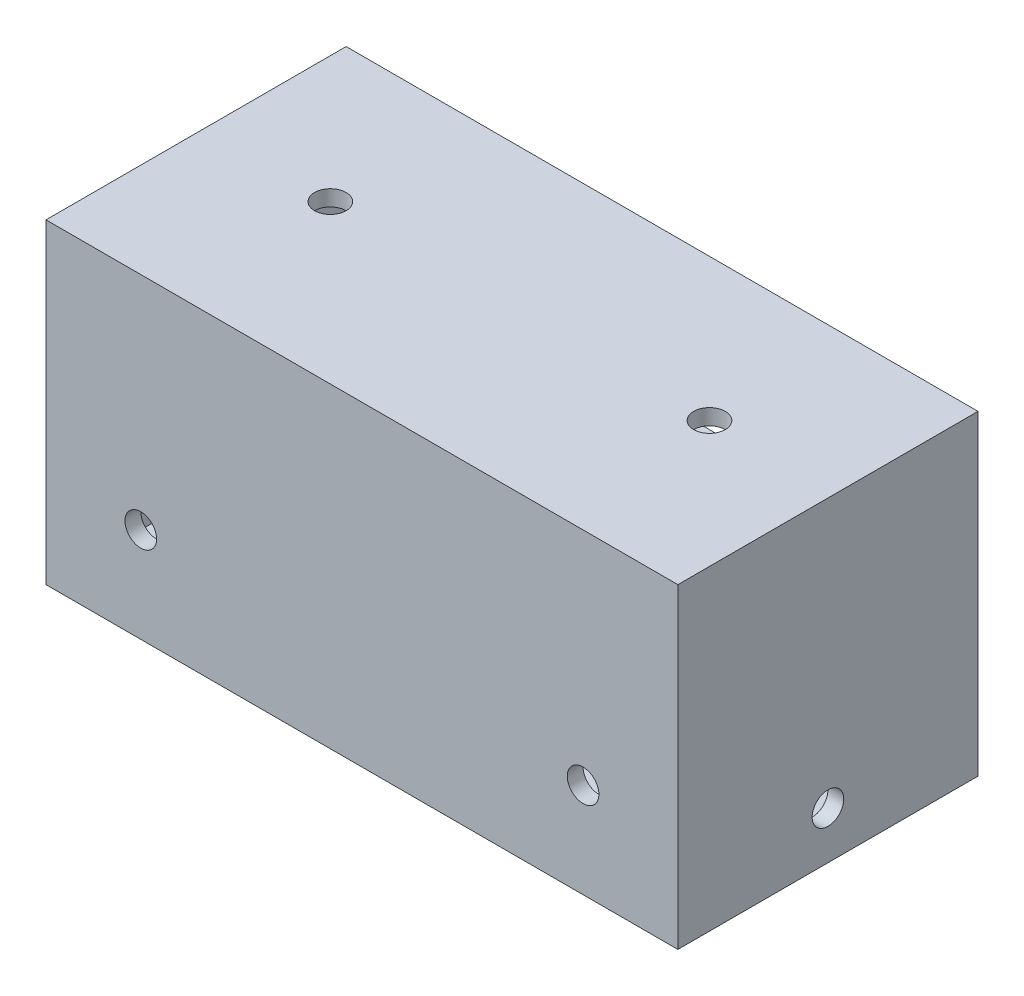
SolidWorks part; units mm, degrees
ref_plane "Front Plane" through (0, 0, 0) normal (0, 0, 1) x (1, 0, 0)
ref_plane "Top Plane" through (0, 0, 0) normal (0, 1, 0) x (1, 0, 0)
ref_plane "Right Plane" through (0, 0, 0) normal (1, 0, 0) x (0, 0, -1)
sketch "Sketch2" plane through (0, 0, 0) normal (0, 0, 1) x (1, 0, 0)
  line L1 (-100, 50) -> (100, 50)
  line L2 (-100, 50) -> (-100, -50)
  line L3 (-100, -50) -> (100, -50)
  line L4 (100, 50) -> (100, -50)
  line L5 (-100, 50) -> (100, -50) construction
  line L6 (-100, -50) -> (100, 50) construction
  line L7 (-95, -45) -> (95, -45)
  line L8 (-95, -45) -> (-95, 45)
  line L9 (-95, 45) -> (95, 45)
  line L10 (95, -45) -> (95, 45)
  line L11 (-95, -45) -> (95, 45) construction
  line L12 (-95, 45) -> (95, -45) construction
  line L13 (-95, -45) -> (-29.0331, -45)
  line L14 (-95, -45) -> (-95, -2.5)
  line L15 (-95, -2.5) -> (-29.0331, -2.5)
  line L16 (-29.0331, -45) -> (-29.0331, -2.5)
  line L17 (-95, 2.5) -> (-29.0331, 2.5)
  line L18 (-95, 2.5) -> (-95, 45)
  line L19 (-95, 45) -> (-29.0331, 45)
  line L20 (-29.0331, 2.5) -> (-29.0331, 45)
  point P0 (0, 0)
  point P6 (0, 0)
  dimension "D1" = 200
  dimension "D2" = 100
  dimension "D3" = 5
  dimension "D4" = 5
  dimension "D5" = 42.5
  dimension "D6" = 42.5
  dimension "D7" = 65.9669
extrude "Boss-Extrude1" add sketch "Sketch2" along normal blind 5 contours L20 L17 L8 L15 L16 L7 L10 L9 | L4 L1 L2 L3 L10 L7 L8 L9 | L7 L16 L15 L8 | L17 L20 L9 L8
sketch "Sketch4" plane through (0, 0, 0) normal (0, 0, -1) x (-1, 0, 0)
  line L0 (-100, 50) -> (-100, -50) construction
  line L1 (95, -45) -> (-95, -45)
  line L2 (95, -45) -> (95, 45)
  line L3 (95, 45) -> (-95, 45)
  line L4 (-95, -45) -> (-95, 45)
  line L5 (95, -45) -> (-95, 45) construction
  line L6 (95, 45) -> (-95, -45) construction
  line L7 (100, -50) -> (-100, -50) construction
  line L9 (95, -45) -> (35, -45)
  line L10 (95, -45) -> (95, -2.5)
  line L11 (95, -2.5) -> (35, -2.5)
  line L12 (35, -45) -> (35, -2.5)
  line L13 (95, 2.5) -> (35, 2.5)
  line L14 (95, 2.5) -> (95, 45)
  line L15 (95, 45) -> (35, 45)
  line L16 (35, 2.5) -> (35, 45)
  line L17 (30, -45) -> (-30, -45)
  line L18 (30, -45) -> (30, -2.5)
  line L19 (30, -2.5) -> (-30, -2.5)
  line L20 (-30, -45) -> (-30, -2.5)
  line L21 (30, 2.5) -> (-30, 2.5)
  line L22 (30, 2.5) -> (30, 45)
  line L23 (30, 45) -> (-30, 45)
  line L24 (-30, 2.5) -> (-30, 45)
  line L25 (-35, -45) -> (-95, -45)
  line L26 (-35, -45) -> (-35, -2.5)
  line L27 (-35, -2.5) -> (-95, -2.5)
  line L28 (-95, -45) -> (-95, -2.5)
  line L29 (-35, 2.5) -> (-95, 2.5)
  line L30 (-35, 2.5) -> (-35, 45)
  line L31 (-35, 45) -> (-95, 45)
  line L32 (-95, 2.5) -> (-95, 45)
  point P0 (0, 0)
  line M18 (-100, 50) -> (-100, -50)
  line M19 (-100, -50) -> (100, -50)
  line M20 (100, -50) -> (100, 50)
  line M21 (100, 50) -> (-100, 50)
  dimension "D1" = 5
  dimension "D2" = 5
  dimension "D3" = 42.5
  dimension "D4" = 42.5
  dimension "D5" = 60
  dimension "D6" = 60
  dimension "D7" = 42.5
  dimension "D8" = 5
  dimension "D9" = 5
  dimension "D10" = 42.5
  dimension "D11" = 60
  dimension "D12" = 60
  dimension "D13" = 5
  dimension "D14" = 5
  dimension "D15" = 42.5
  dimension "D16" = 42.5
extrude "Boss-Extrude2" add sketch "Sketch4" along normal blind 90 contours L1 L4 L3 L2 M21 M18 M19 M20 | L30 L29 L4 L27 L26 L1 L20 L19 L18 L12 L11 L2 L13 L16 L3 L22 L21 L24
sketch "Sketch5" plane through (-35, 0, 0) normal (-1, 0, 0) x (0, 0, 1)
  line L0 (0, 2.5) -> (0, 45) construction
  line L1 (-10, 12.5) -> (-80, 12.5)
  line L2 (-10, 12.5) -> (-10, 35)
  line L3 (-10, 35) -> (-80, 35)
  line L4 (-80, 12.5) -> (-80, 35)
  line L5 (-90, 2.5) -> (0, 2.5) construction
  line L6 (-90, 45) -> (0, 45) construction
  line L7 (-90, 2.5) -> (-90, 45) construction
  dimension "D1" = 10
  dimension "D2" = 10
  dimension "D3" = 10
  dimension "D4" = 10
extrude "Cut-Extrude1" cut sketch "Sketch5" against normal blind 90
sketch "Sketch6" plane through (-35, 0, 0) normal (-1, 0, 0) x (0, 0, 1)
  line L0 (-90, -45) -> (-90, -2.5) construction
  line L1 (-10, -35) -> (-80, -35)
  line L2 (-10, -35) -> (-10, -12.5)
  line L3 (-10, -12.5) -> (-80, -12.5)
  line L4 (-80, -35) -> (-80, -12.5)
  line L5 (-90, -45) -> (0, -45) construction
  line L6 (-90, -2.5) -> (0, -2.5) construction
  line L7 (0, -45) -> (0, -2.5) construction
  dimension "D1" = 10
  dimension "D2" = 10
  dimension "D3" = 10
  dimension "D4" = 10
extrude "Cut-Extrude2" cut sketch "Sketch6" against normal blind 90
sketch "Sketch7" plane through (0, -2.5, 0) normal (0, -1, 0) x (-1, 0, 0)
  line L0 (95, 90) -> (35, 90) construction
  line L1 (85, 10) -> (45, 10)
  line L2 (85, 10) -> (85, 80)
  line L3 (85, 80) -> (45, 80)
  line L4 (45, 10) -> (45, 80)
  line L5 (95, 0) -> (35, 0) construction
  line L6 (35, 90) -> (35, 0) construction
  line L7 (95, 90) -> (95, 0) construction
  dimension "D1" = 10
  dimension "D2" = 10
  dimension "D3" = 10
  dimension "D4" = 10
extrude "Cut-Extrude3" cut sketch "Sketch7" against normal blind 10
sketch "Sketch8" plane through (0, -2.5, 0) normal (0, -1, 0) x (-1, 0, 0)
  line L0 (30, 0) -> (-30, 0) construction
  line L1 (20, 10) -> (-20, 10)
  line L2 (20, 10) -> (20, 80)
  line L3 (20, 80) -> (-20, 80)
  line L4 (-20, 10) -> (-20, 80)
  line L5 (-30, 90) -> (-30, 0) construction
  line L6 (30, 90) -> (-30, 90) construction
  line L7 (30, 90) -> (30, 0) construction
  dimension "D1" = 10
  dimension "D2" = 10
  dimension "D3" = 10
  dimension "D4" = 10
extrude "Cut-Extrude4" cut sketch "Sketch8" against normal blind 10
sketch "Sketch9" plane through (0, -2.5, 0) normal (0, -1, 0) x (-1, 0, 0)
  line L0 (-35, 90) -> (-35, 0) construction
  line L1 (-45, 10) -> (-85, 10)
  line L2 (-45, 10) -> (-45, 80)
  line L3 (-45, 80) -> (-85, 80)
  line L4 (-85, 10) -> (-85, 80)
  line L5 (-35, 90) -> (-95, 90) construction
  line L6 (-35, 0) -> (-95, 0) construction
  line L7 (-95, 90) -> (-95, 0) construction
  dimension "D1" = 10
  dimension "D2" = 10
  dimension "D3" = 10
  dimension "D4" = 10
extrude "Cut-Extrude5" cut sketch "Sketch9" against normal blind 10
sketch "Sketch10" plane through (0, 0, -90) normal (0, 0, -1) x (-1, 0, 0)
  line L0 (30, -2.5) -> (-30, -2.5) construction
  line L1 (35, -45) -> (35, -2.5) construction
  line L2 (-100, -50) -> (100, -50) construction
  line L3 (100, -50) -> (100, 50) construction
  line L4 (0, 0) -> (0, -50) construction
  line L5 (0, 0) -> (100, 0) construction
  line L6 (-100, 50) -> (-100, -50) construction
  circle A0 centre (32.5, 0) radius 2
  circle A1 centre (97.5, -47.5) radius 2
  circle A2 centre (97.5, 47.5) radius 2
  circle A3 centre (-97.5, 47.5) radius 2
  circle A4 centre (-32.5, 0) radius 2
  circle A5 centre (-97.5, -47.5) radius 2
  dimension "D3" = 4
  dimension "D6" = 4
  dimension "D1" = 2.5
  dimension "D2" = 2.5
  dimension "D4" = 2.5
  dimension "D5" = 2.5
extrude "Cut-Extrude6" cut sketch "Sketch10" against normal blind 10
sketch "Sketch11" plane through (0, -50, 0) normal (0, -1, 0) x (-1, 0, 0)
  line L0 (100, -5) -> (-100, -5) construction
  line L3 (100, -5) -> (100, 90) construction
  line L8 (-100, -5) -> (-100, 90) construction
  circle A0 centre (60, 45) radius 5
  circle A1 centre (-60, 45) radius 5
  dimension "D1" = 10
  dimension "D6" = 10
  dimension "D2" = 50
  dimension "D3" = 50
  dimension "D4" = 40
  dimension "D5" = 40
extrude "Cut-Extrude7" cut sketch "Sketch11" against normal blind 150
sketch "Sketch12" plane through (-100, 0, 0) normal (-1, 0, 0) x (0, 0, 1)
  line L0 (-42.5, -50) -> (-42.5, 50) construction
  line L1 (5, -50) -> (-90, -50) construction
  line L2 (5, 50) -> (-90, 50) construction
  circle A0 centre (-42.5, -35) radius 5
  dimension "D1" = 10
  dimension "D2" = 15
extrude "Cut-Extrude8" cut sketch "Sketch12" against normal blind 10
sketch "Sketch13" plane through (100, 0, 0) normal (1, 0, 0) x (0, 0, -1)
  line L0 (42.5, -50) -> (42.5, 50) construction
  line L1 (-5, -50) -> (90, -50) construction
  line L2 (-5, 50) -> (90, 50) construction
  circle A0 centre (42.5, -35) radius 5
  dimension "D2" = 10
  dimension "D1" = 15
extrude "Cut-Extrude9" cut sketch "Sketch13" against normal blind 10
sketch "Sketch14" plane through (0, 0, 5) normal (0, 0, 1) x (1, 0, 0)
  line L0 (0, 50) -> (0, -50) construction
  line L1 (-100, 50) -> (100, 50) construction
  line L2 (-100, -50) -> (100, -50) construction
  line L3 (-100, 50) -> (-100, -50) construction
  circle A0 centre (-70, -20) radius 5
  circle A1 centre (70, -20) radius 5
  dimension "D1" = 10
  dimension "D2" = 30
  dimension "D3" = 30
extrude "Cut-Extrude10" cut sketch "Sketch14" against normal blind 10
sketch "Sketch16" plane through (0, -50, 0) normal (0, -1, 0) x (1, 0, 0)
  line L0 (100, -45) -> (-100, -45) construction
  line L1 (100, 5) -> (100, -90) construction
  line L2 (-100, 5) -> (-100, -90) construction
  line L3 (-100, 5) -> (100, 5) construction
  line L5 (0, -45) -> (0, 5) construction
  line L6 (100, -15.6846) -> (90, -5) construction
  line L7 (100, -15.6846) -> (90, -5) construction
  line L8 (90, -5) -> (80.6407, 5) construction
  circle A0 centre (90, -5) radius 0.2
  circle A1 centre (91.7083, -6.8253) radius 0.2
  circle A2 centre (88.2917, -3.1747) radius 0.2
  circle A3 centre (-91.7083, -6.8253) radius 0.2
  circle A4 centre (-90, -5) radius 0.2
  circle A5 centre (-88.2917, -3.1747) radius 0.2
  circle A6 centre (88.2917, -86.8253) radius 0.2
  circle A7 centre (90, -85) radius 0.2
  circle A8 centre (91.7083, -83.1747) radius 0.2
  circle A9 centre (-88.2917, -86.8253) radius 0.2
  circle A10 centre (-90, -85) radius 0.2
  circle A11 centre (-91.7083, -83.1747) radius 0.2
  dimension "D3" = 0.4
  dimension "D6" = 0.4
  dimension "D7" = 0.4
  dimension "D1" = 50
  dimension "D2" = 200
  dimension "D4" = 10
  dimension "D5" = 10
  dimension "D8" = 2.5
  dimension "D9" = 19.3593
  dimension "D10" = 2.5
extrude "Cut-Extrude11" cut sketch "Sketch16" against normal blind 10
sketch "Sketch17" plane through (0, 0, -10) normal (0, 0, -1) x (-1, 0, 0)
  line L1 (85, -2.5) -> (45, -2.5)
  line L2 (85, -2.5) -> (85, 2.5)
  line L3 (85, 2.5) -> (45, 2.5)
  line L4 (45, -2.5) -> (45, 2.5)
extrude "Boss-Extrude3" add sketch "Sketch17" along normal blind 70
sketch "Sketch18" plane through (0, 0, -10) normal (0, 0, -1) x (-1, 0, 0)
  line L1 (-45, -2.5) -> (-85, -2.5)
  line L2 (-45, -2.5) -> (-45, 2.5)
  line L3 (-45, 2.5) -> (-85, 2.5)
  line L4 (-85, -2.5) -> (-85, 2.5)
extrude "Boss-Extrude4" add sketch "Sketch18" along normal blind 70
